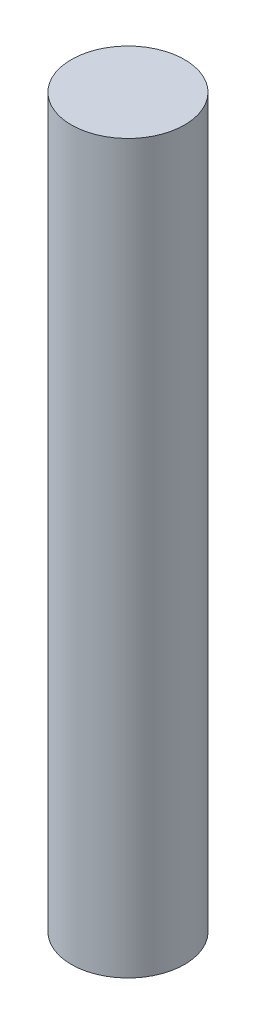
SolidWorks part; units mm, degrees
material "6061-T6 (SS)"
ref_plane "Front Plane" through (0, 0, 0) normal (0, 0, 1) x (1, 0, 0)
ref_plane "Top Plane" through (0, 0, 0) normal (0, 1, 0) x (1, 0, 0)
ref_plane "Right Plane" through (0, 0, 0) normal (1, 0, 0) x (0, 0, -1)
sketch "Sketch1" plane through (0, 0, 0) normal (0, 1, 0) x (1, 0, 0)
  circle A0 centre (0, 0) radius 4
  dimension "D1" = 8
extrude "Boss-Extrude1" add sketch "Sketch1" along normal mid plane 51.35
